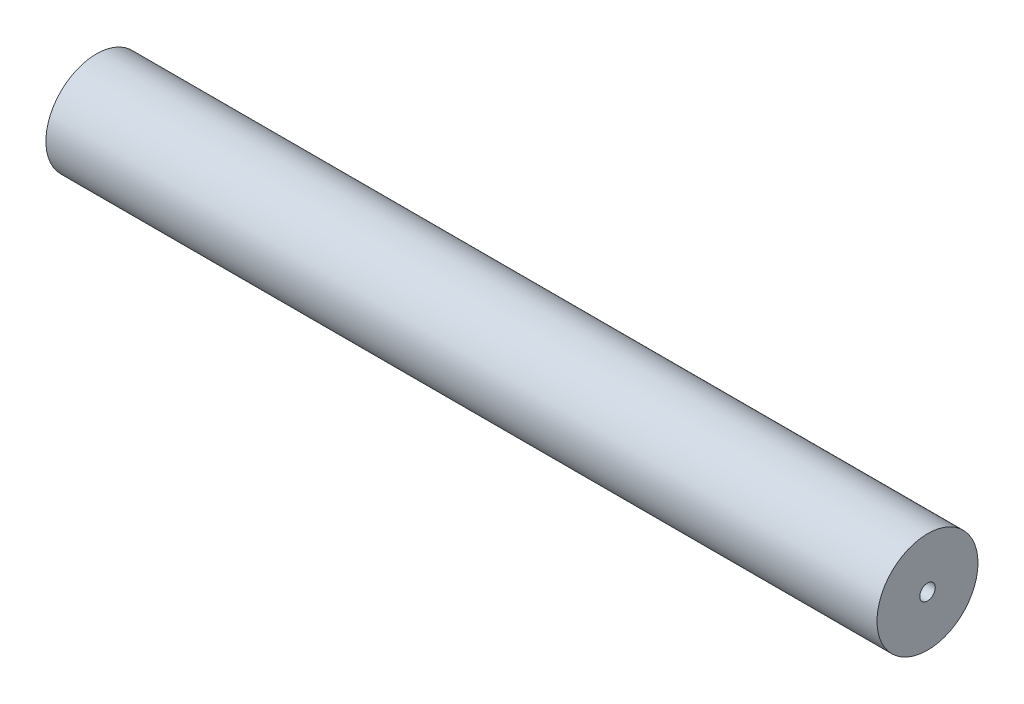
SolidWorks part; units mm, degrees
material "AISI 316 Annealed Stainless Steel Bar (SS)"
ref_plane "Front Plane" through (0, 0, 0) normal (0, 0, 1) x (1, 0, 0)
ref_plane "Top Plane" through (0, 0, 0) normal (0, 1, 0) x (1, 0, 0)
ref_plane "Right Plane" through (0, 0, 0) normal (1, 0, 0) x (0, 0, -1)
sketch "Sketch1" plane through (0, 0, 0) normal (0, 0, 1) x (1, 0, 0)
  line L1 (11, 0.5) -> (11, 3.25)
  line L2 (11, 3.25) -> (-41.3, 3.25) construction
  line L3 (10, 0.5) -> (11, 0.5)
  line L4 (10, 0.5) -> (10, 2.25)
  line L5 (10, 2.25) -> (-42.5, 2.25)
  line L7 (-42.5, 5.25) -> (-41.3, 5.25) construction
  line L8 (-41.3, 5.25) -> (-41.3, 3.25) construction
  line L9 (-42.5, 2.25) -> (-42.5, 5.25) construction
  line L10 (11, 3.25) -> (-42.5, 3.25)
  line L11 (-42.5, 3.25) -> (-42.5, 2.25)
  dimension "D1" = 3.25
  dimension "D2" = 2.75
  dimension "D3" = 1
  dimension "D4" = 1
  dimension "D5" = 3
  dimension "D6" = 10
  dimension "D7" = 1.2
  dimension "D8" = 53.5
ref_axis "Axis1" through (13.5, 0, 0) along (-1, 0, 0)
revolve "Revolve1" add sketch "Sketch1" angle 360 about axis through (13.5, 0, 0) along (-1, 0, 0)
